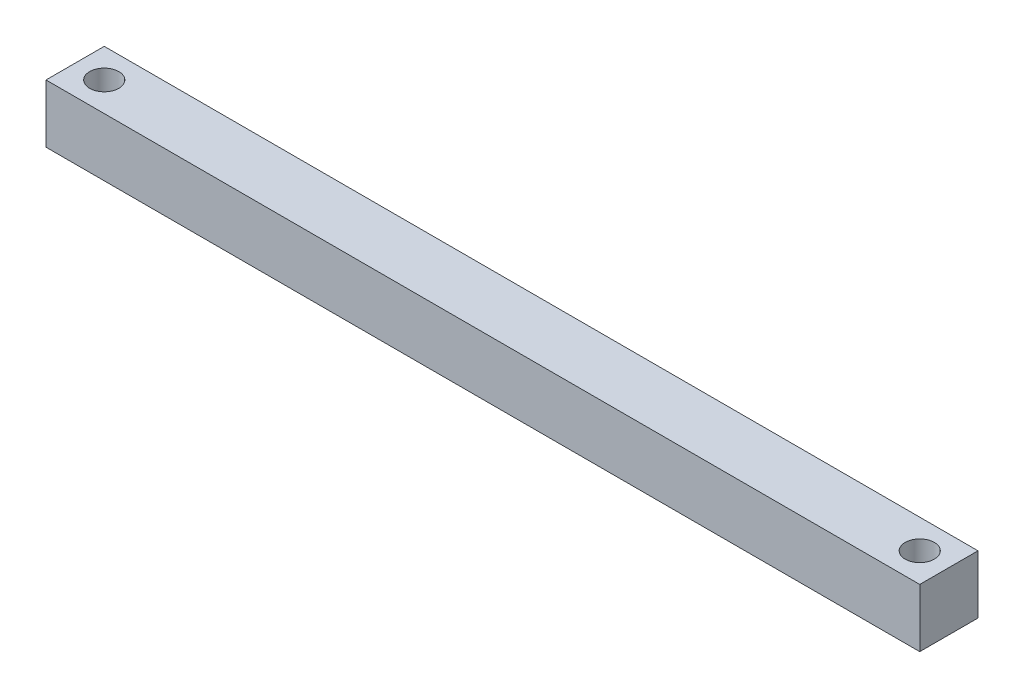
SolidWorks part; units mm, degrees
ref_plane "Front Plane" through (0, 0, 0) normal (0, 0, 1) x (1, 0, 0)
ref_plane "Top Plane" through (0, 0, 0) normal (0, 1, 0) x (1, 0, 0)
ref_plane "Right Plane" through (0, 0, 0) normal (1, 0, 0) x (0, 0, -1)
sketch "Sketch1" plane through (0, 0, 0) normal (1, 0, 0) x (0, 0, -1)
  line L1 (0, 0) -> (-25.4, 0)
  line L2 (0, 0) -> (0, 25.4)
  line L3 (0, 25.4) -> (-25.4, 25.4)
  line L4 (-25.4, 0) -> (-25.4, 25.4)
  dimension "D1" = 25.4
  dimension "D2" = 25.4
extrude "Boss-Extrude1" add sketch "Sketch1" along normal blind 381
sketch "Sketch2" plane through (0, 25.4, 0) normal (0, 1, 0) x (1, 0, 0)
  line L0 (381, 0) -> (0, 0) construction
  line L1 (381, 0) -> (381, -25.4) construction
  line L2 (0, 0) -> (0, -25.4) construction
  line L3 (381, -25.4) -> (0, -25.4) construction
  circle A0 centre (368.3, -12.7) radius 6.35
  circle A1 centre (12.7, -12.7) radius 6.35
  point P10 (0, -12.7)
  dimension "D1" = 12.7
  dimension "D2" = 12.7
  dimension "D3" = 12.7
  dimension "D4" = 12.7
  dimension "D5" = 12.7
  dimension "D6" = 12.7
extrude "Cut-Extrude1" cut sketch "Sketch2" against normal through all
